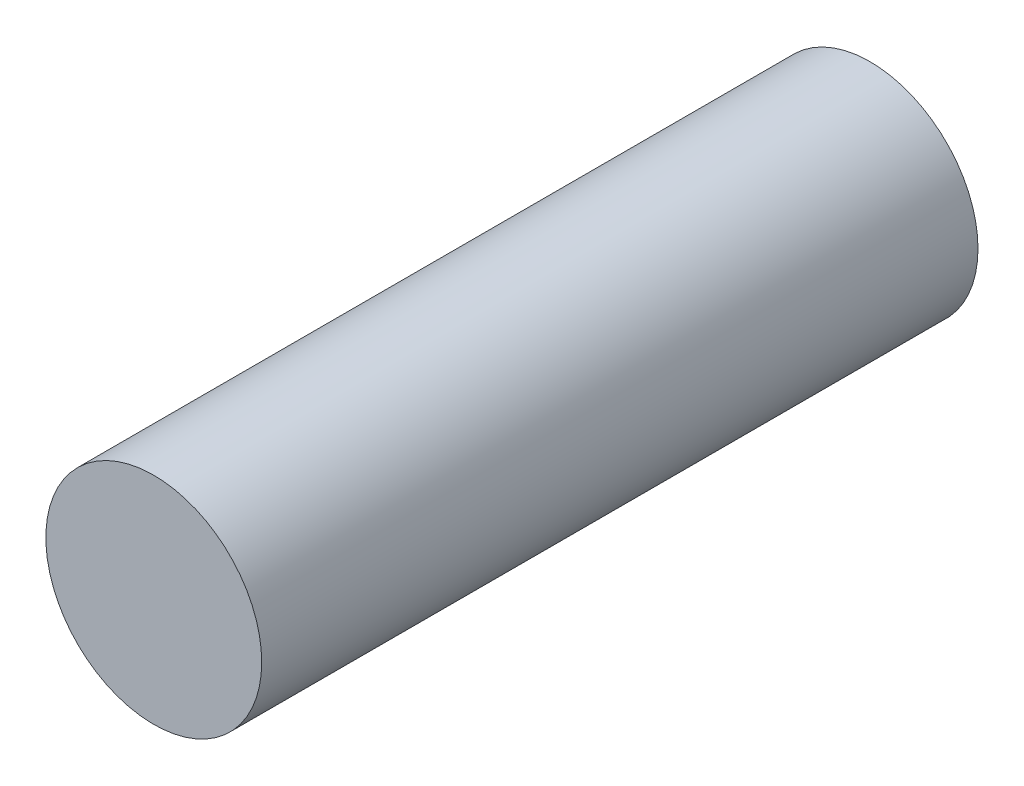
SolidWorks part; units mm, degrees
ref_plane "Ön Düzlem" through (0, 0, 0) normal (1, 0, 0) x (0, 1, 0)
ref_plane "Üst Düzlem" through (0, 0, 0) normal (0, 0, 1) x (0, 1, 0)
ref_plane "Sağ Düzlem" through (0, 0, 0) normal (0, 1, 0) x (-1, 0, 0)
sketch "Çizim1" plane through (0, 0, 0) normal (0, 0, 1) x (0, 1, 0)
  circle A0 centre (0, 0) radius 11
extrude "Yükseklik-Ekstrüzyon1" add sketch "Çizim1" along normal blind 73
